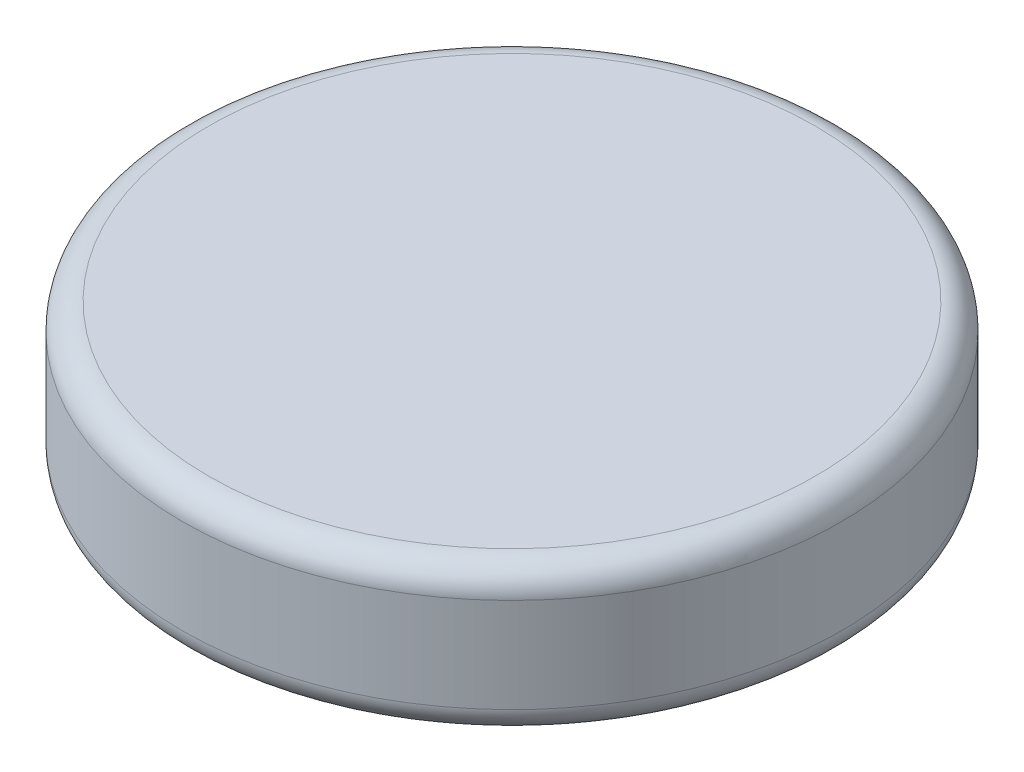
SolidWorks part; units mm, degrees
ref_plane "Front Plane" through (0, 0, 0) normal (0, 0, 1) x (1, 0, 0)
ref_plane "Top Plane" through (0, 0, 0) normal (0, 1, 0) x (1, 0, 0)
ref_plane "Right Plane" through (0, 0, 0) normal (1, 0, 0) x (0, 0, -1)
sketch "Sketch1" plane through (0, 0, 0) normal (0, 1, 0) x (1, 0, 0)
  circle A0 centre (0, 0) radius 15.9385
  dimension "D1" = 31.877
extrude "Boss-Extrude1" add sketch "Sketch1" along normal blind 7.112 contours A0
fillet "Fillet1" radius 1.27 2 edges at (0, 0, 15.9385) (0, 7.112, 15.9385)
